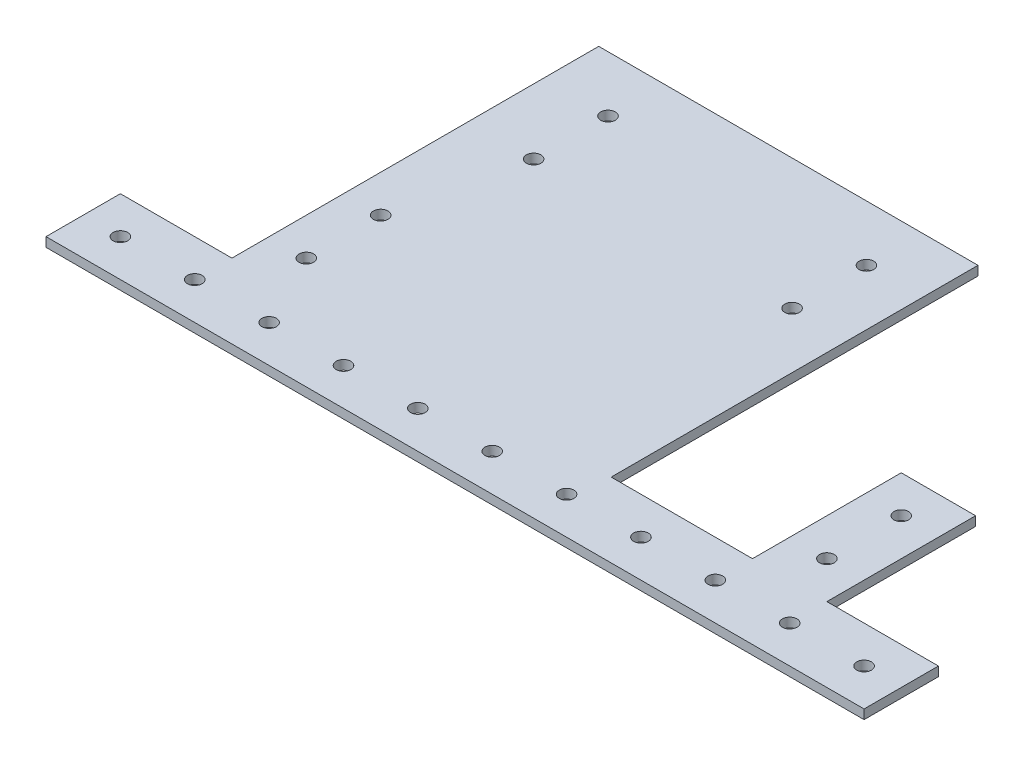
SolidWorks part; units mm, degrees
material "6061-T6 (SS)"
ref_plane "Front Plane" through (0, 0, 0) normal (0, 0, 1) x (1, 0, 0)
ref_plane "Top Plane" through (0, 0, 0) normal (0, 1, 0) x (1, 0, 0)
ref_plane "Right Plane" through (0, 0, 0) normal (1, 0, 0) x (0, 0, -1)
sketch "Sketch1" plane through (0, 0, 0) normal (0, 1, 0) x (1, 0, 0)
  line L0 (139.7, 0) -> (-139.7, 0)
  line L2 (-101.6, 150.6728) -> (27.94, 150.6728)
  line L3 (27.94, 150.6728) -> (27.94, 25.4)
  line L4 (27.94, 25.4) -> (76.2, 25.4)
  line L5 (76.2, 25.4) -> (76.2, 76.2)
  line L6 (76.2, 76.2) -> (101.6, 76.2)
  line L8 (-139.7, 0) -> (-139.7, 25.4)
  line L9 (-139.7, 25.4) -> (-101.6, 25.4)
  line L10 (-101.6, 25.4) -> (-101.6, 150.6728)
  line L11 (139.7, 0) -> (139.7, 25.4)
  line L12 (139.7, 25.4) -> (101.6, 25.4)
  line L14 (101.6, 25.4) -> (101.6, 76.2)
  line L15 (-139.7, 12.7) -> (139.7, 12.7) construction
  line L16 (-88.9, 0) -> (-88.9, 150.6728) construction
  line L17 (88.9, 76.2) -> (88.9, 0) construction
  line L18 (-101.6, 87.1728) -> (27.94, 87.1728) construction
  line L19 (-79.375, 106.2228) -> (8.89, 106.2228) construction
  line L20 (-79.375, 106.2228) -> (-79.375, 131.6228) construction
  line L21 (-79.375, 131.6228) -> (8.89, 131.6228) construction
  line L22 (8.89, 106.2228) -> (8.89, 131.6228) construction
  line L23 (-35.2425, 131.6228) -> (-35.2425, 150.6728) construction
  line L24 (-35.2425, 106.2228) -> (-35.2425, 87.1728) construction
  circle A0 centre (-127, 12.7) radius 2.4892
  circle A1 centre (-88.9, 38.1) radius 2.4892
  circle A2 centre (-88.9, 63.5) radius 2.4892
  circle A3 centre (-79.375, 131.6228) radius 2.4892
  circle A4 centre (-79.375, 106.2228) radius 2.4892
  circle A5 centre (8.89, 106.2228) radius 2.4892
  circle A6 centre (8.89, 131.6228) radius 2.4892
  circle A7 centre (88.9, 63.5) radius 2.4892
  circle A8 centre (88.9, 38.1) radius 2.4892
  circle A9 centre (-101.6, 12.7) radius 2.4892
  circle A10 centre (-76.2, 12.7) radius 2.4892
  circle A11 centre (-50.8, 12.7) radius 2.4892
  circle A12 centre (-25.4, 12.7) radius 2.4892
  circle A13 centre (0, 12.7) radius 2.4892
  circle A14 centre (25.4, 12.7) radius 2.4892
  circle A15 centre (50.8, 12.7) radius 2.4892
  circle A16 centre (76.2, 12.7) radius 2.4892
  circle A17 centre (101.6, 12.7) radius 2.4892
  circle A18 centre (127, 12.7) radius 2.4892
  point P4 (0, 0)
  dimension "D9" = 4.9784
  dimension "D10" = 12.7
  dimension "D13" = 12.7
  dimension "D14" = 25.4
  dimension "D1" = 76.2
  dimension "D2" = 25.4
  dimension "D3" = 25.4
  dimension "D4" = 129.54
  dimension "D5" = 38.1
  dimension "D6" = 279.4
  dimension "D7" = 150.6728
  dimension "D8" = 25.4
  dimension "D12" = 12.7
  dimension "D15" = 19.05
  dimension "D16" = 63.5
  dimension "D17" = 22.225
  dimension "D11" = 11
extrude "Boss-Extrude1" add sketch "Sketch1" along normal blind 3.175
